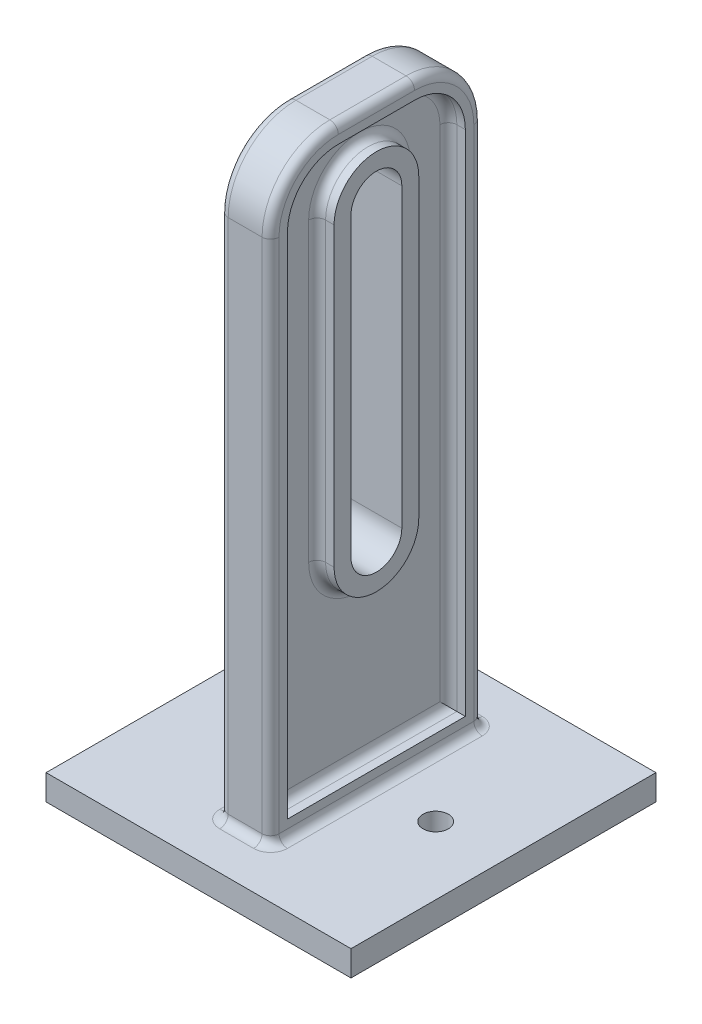
SolidWorks part; units mm, degrees
ref_plane "Front Plane" through (0, 0, 0) normal (0, 0, 1) x (1, 0, 0)
ref_plane "Top Plane" through (0, 0, 0) normal (0, 1, 0) x (1, 0, 0)
ref_plane "Right Plane" through (0, 0, 0) normal (1, 0, 0) x (0, 0, -1)
sketch "Sketch1" plane through (0, 0, 0) normal (0, 1, 0) x (1, 0, 0)
  line L1 (18, -18) -> (-18, -18)
  line L2 (18, -18) -> (18, 18)
  line L3 (18, 18) -> (-18, 18)
  line L4 (-18, -18) -> (-18, 18)
  line L5 (18, -18) -> (-18, 18) construction
  line L6 (18, 18) -> (-18, -18) construction
  point P0 (0, 0)
  dimension "D1" = 36
extrude "Boss-Extrude1" add sketch "Sketch1" along normal blind 3
sketch "Sketch2" plane through (0, 3, 0) normal (0, 1, 0) x (1, 0, 0)
  line L0 (13.1687, 0) -> (-14.1019, 0) construction
  line L1 (0, 15.2943) -> (0, -13.5316) construction
  circle A0 centre (-10, 0) radius 1.5
  circle A1 centre (10, 0) radius 1.5
  point P9 (0, 0)
  dimension "D1" = 3
  dimension "D2" = 20
extrude "Cut-Extrude1" cut sketch "Sketch2" against normal blind 3
sketch "Sketch3" plane through (0, 3, 0) normal (0, 1, 0) x (1, 0, 0)
  line L1 (3, -12.5) -> (-3, -12.5)
  line L2 (3, -12.5) -> (3, 12.5)
  line L3 (3, 12.5) -> (-3, 12.5)
  line L4 (-3, -12.5) -> (-3, 12.5)
  line L5 (3, -12.5) -> (-3, 12.5) construction
  line L6 (3, 12.5) -> (-3, -12.5) construction
  point P0 (0, 0)
  dimension "D1" = 25
  dimension "D2" = 6
extrude "Boss-Extrude2" add sketch "Sketch3" along normal blind 70
sketch "Sketch4" plane through (3, 0, 0) normal (1, 0, 0) x (0, 0, -1)
  line L0 (0, 63) -> (0, 28) construction
  line L1 (3, 63) -> (3, 28)
  line L2 (-3, 63) -> (-3, 28)
  line L3 (-12.5, 73) -> (12.5, 73) construction
  arc A0 (3, 63) -> (-3, 63) centre (0, 63) ccw
  arc A1 (-3, 28) -> (3, 28) centre (0, 28) ccw
  point P3 (0, 45.5)
  dimension "D1" = 3
  dimension "D2" = 10
  dimension "D3" = 35
extrude "Cut-Extrude2" cut sketch "Sketch4" against normal blind 70
fillet "Fillet1" radius 8 2 edges at (0, 73, -12.5) (0, 73, 12.5)
sketch "Sketch8" plane through (3, 0, 0) normal (1, 0, 0) x (0, 0, -1)
  line L8 (5, 28) -> (5, 63)
  line L9 (-5, 63) -> (-5, 28)
  line L10 (5, 28) -> (5, 63) construction
  line L11 (-5, 63) -> (-5, 28) construction
  line L12 (-10.5, 65) -> (-10.5, 5)
  line L13 (-10.5, 5) -> (10.5, 5)
  line L14 (10.5, 5) -> (10.5, 65)
  line L15 (4.5, 71) -> (-4.5, 71)
  line L27 (5, 63) -> (5, 28)
  line L28 (-5, 63) -> (-5, 28)
  line L39 (-10.5, 5) -> (10.5, 5)
  line L40 (10.5, 5) -> (10.5, 65)
  line L41 (4.5, 71) -> (-4.5, 71)
  line L42 (-10.5, 65) -> (-10.5, 5)
  line L43 (-10.5, 5) -> (10.5, 5) construction
  line L44 (10.5, 5) -> (10.5, 65) construction
  line L45 (4.5, 71) -> (-4.5, 71) construction
  line L46 (-10.5, 65) -> (-10.5, 5) construction
  arc A6 (-5, 28) -> (5, 28) centre (0, 28) ccw
  arc A7 (5, 63) -> (-5, 63) centre (0, 63) ccw
  arc A8 (-5, 28) -> (5, 28) centre (0, 28) ccw construction
  arc A9 (5, 63) -> (-5, 63) centre (0, 63) ccw construction
  arc A10 (-10.5, 65) -> (-4.5, 71) centre (-4.5, 65) cw
  arc A11 (4.5, 71) -> (10.5, 65) centre (4.5, 65) cw
  arc A12 (5, 63) -> (-5, 63) centre (0, 63) ccw
  arc A13 (-5, 28) -> (5, 28) centre (0, 28) ccw
  arc A26 (10.5, 65) -> (4.5, 71) centre (4.5, 65) ccw
  arc A27 (-4.5, 71) -> (-10.5, 65) centre (-4.5, 65) ccw
  arc A28 (10.5, 65) -> (4.5, 71) centre (4.5, 65) ccw construction
  arc A29 (-4.5, 71) -> (-10.5, 65) centre (-4.5, 65) ccw construction
  dimension "D1" = 2
  dimension "D4" = 2
extrude "Cut-Extrude5" cut sketch "Sketch8" against normal blind 2
mirror "Mirror1" about plane through (0, 0, 0) normal (1, 0, 0) of "Cut-Extrude5"
fillet "Fillet3" radius 1 10 edges at (3, 34, 12.5) (3, 70.6569, 10.1569) (3, 73, 0) (3, 70.6569, -10.1569) (3, 34, -12.5) (-3, 34, 12.5) (-3, 70.6569, 10.1569) (-3, 73, 0) (-3, 70.6569, -10.1569) (-3, 34, -12.5)
fillet "Fillet4" radius 1 20 edges at (-1, 45.5, -5) (-1, 23, 0) (-1, 45.5, 5) (-1, 68, 0) (-1, 69.2426, -8.7426) (-1, 71, 0) (-1, 69.2426, 8.7426) (-1, 35, 10.5) (-1, 35, -10.5) (-1, 5, 0) (1, 23, 0) (1, 45.5, 5) (1, 68, 0) (1, 45.5, -5) (1, 5, 0) (1, 71, 0) (1, 69.2426, -8.7426) (1, 35, -10.5) (1, 69.2426, 8.7426) (1, 35, 10.5)
fillet "Fillet5" radius 1 8 edges at (-2.7071, 3, 12.2071) (0, 3, 12.5) (2.7071, 3, 12.2071) (-2.7071, 3, -12.2071) (-3, 3, 0) (0, 3, -12.5) (2.7071, 3, -12.2071) (3, 3, 0)
